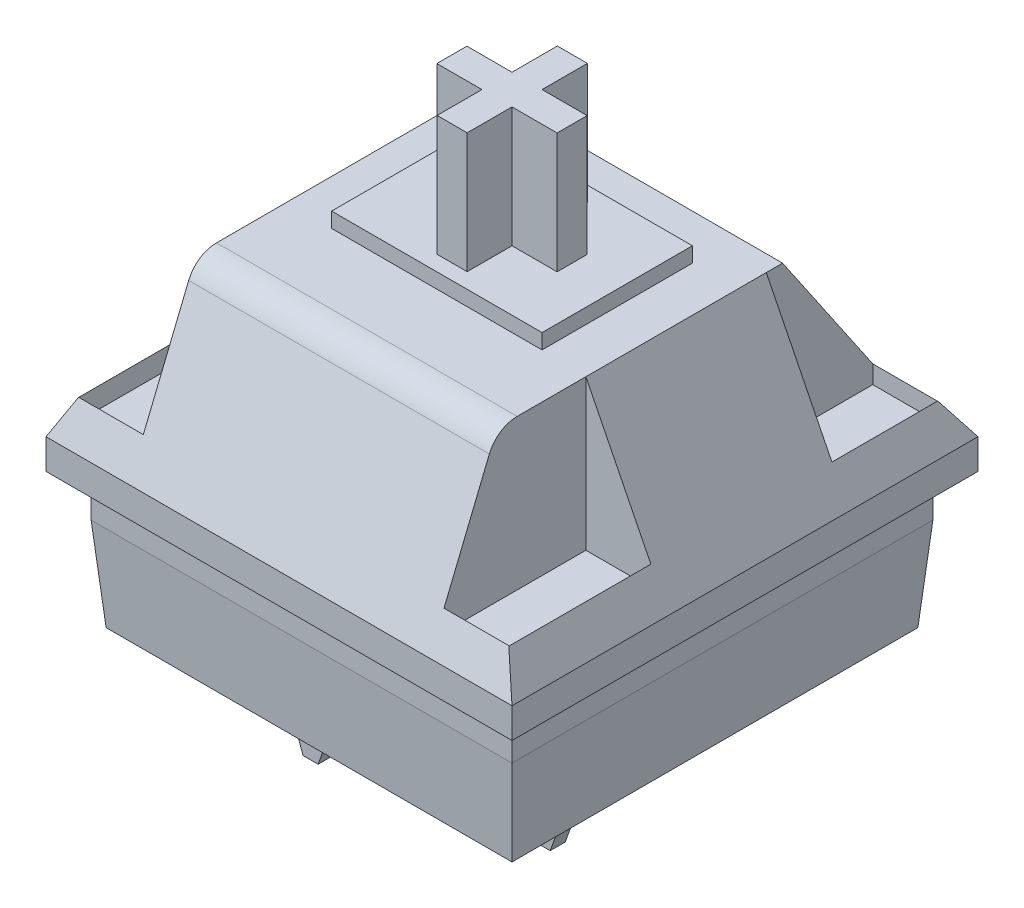
SolidWorks part; units mm, degrees
ref_plane "前视基准面" through (0, 0, 0) normal (0, 0, 1) x (1, 0, 0)
ref_plane "上视基准面" through (0, 0, 0) normal (0, 1, 0) x (1, 0, 0)
ref_plane "右视基准面" through (0, 0, 0) normal (1, 0, 0) x (0, 0, -1)
sketch "草图1" plane through (0, 0, 0) normal (0, 1, 0) x (1, 0, 0)
  line L1 (-6.75, 6.75) -> (6.75, 6.75)
  line L2 (-6.75, 6.75) -> (-6.75, -6.75)
  line L3 (-6.75, -6.75) -> (6.75, -6.75)
  line L4 (6.75, 6.75) -> (6.75, -6.75)
  line L5 (-6.75, 6.75) -> (6.75, -6.75) construction
  line L6 (-6.75, -6.75) -> (6.75, 6.75) construction
  point P0 (0, 0)
  dimension "D1" = 13.5
  dimension "D2" = 13.5
ref_plane "基准面1" through (0, 4.5, 0) normal (0, 1, 0) x (1, 0, 0)
sketch "草图2" plane through (0, 4.5, 0) normal (0, 1, 0) x (1, 0, 0)
  line L1 (-7, 7) -> (7, 7)
  line L2 (-7, 7) -> (-7, -7)
  line L3 (-7, -7) -> (7, -7)
  line L4 (7, 7) -> (7, -7)
  line L5 (-7, 7) -> (7, -7) construction
  line L6 (-7, -7) -> (7, 7) construction
  point P0 (0, 0)
  dimension "D1" = 14
  dimension "D2" = 14
ref_plane "基准面2" through (0, -0.3738, -6.7292) normal (0, -0.0555, -0.9985) x (-1, 0, 0)
extrude "凸台-拉伸1" add sketch "草图2" against normal blind 1.4
loft "放样2" add profiles "草图1" section face at (0, 3.1, 0) section "草图1"
sketch "草图8" plane through (0, 4.5, 0) normal (0, 1, 0) x (1, 0, 0)
  line L1 (7.75, -7.75) -> (-7.75, -7.75)
  line L2 (7.75, -7.75) -> (7.75, 7.75)
  line L3 (7.75, 7.75) -> (-7.75, 7.75)
  line L4 (-7.75, -7.75) -> (-7.75, 7.75)
  line L5 (7.75, -7.75) -> (-7.75, 7.75) construction
  line L6 (7.75, 7.75) -> (-7.75, -7.75) construction
  point P0 (0, 0)
  dimension "D1" = 15.5
  dimension "D2" = 15.5
extrude "凸台-拉伸2" add sketch "草图8" along normal blind 1
ref_plane "基准面8" through (0, 11, 0) normal (0, 1, 0) x (1, 0, 0)
sketch "草图10" plane through (0, 11, 0) normal (0, 1, 0) x (1, 0, 0)
  line L0 (-5, 0) -> (5, 0) construction
  line L1 (-5, 4) -> (5, 4)
  line L2 (-5, 4) -> (-5, -5.5)
  line L3 (-5, -5.5) -> (5, -5.5)
  line L4 (5, 4) -> (5, -5.5)
  point P4 (0, 0)
  point P5 (0, 0)
  dimension "D1" = 10
  dimension "D2" = 5.5
  dimension "D3" = 4
loft "放样6" add profiles "草图10" section face at (0, 5.5, 0) section "草图10"
ref_plane "基准面9" through (0, 11, 0) normal (0, 1, 0) x (1, 0, 0)
sketch "草图12" plane through (0, 11, 0) normal (0, 1, 0) x (1, 0, 0)
  line L1 (-3.5, -2.5) -> (3.5, -2.5)
  line L2 (-3.5, -2.5) -> (-3.5, 2.5)
  line L3 (-3.5, 2.5) -> (3.5, 2.5)
  line L4 (3.5, -2.5) -> (3.5, 2.5)
  line L5 (-3.5, -2.5) -> (3.5, 2.5) construction
  line L6 (-3.5, 2.5) -> (3.5, -2.5) construction
  point P0 (0, 0)
  dimension "D1" = 5
  dimension "D2" = 7
extrude "凸台-拉伸3" add sketch "草图12" along normal blind 0.5
ref_plane "基准面10" through (0, 11.5, 0) normal (0, 1, 0) x (1, 0, 0)
sketch "草图14" plane through (0, 11.5, 0) normal (0, 1, 0) x (1, 0, 0)
  line L0 (0, 2.7022) -> (0, 2.0086) construction
  line L1 (-3.5, 0) -> (-2, 0) construction
  line L2 (-3.5, 2.5) -> (-3.5, -2.5) construction
  line L3 (3.5, -2.5) -> (3.5, 2.5) construction
  line L4 (0.5, -0.5) -> (2, -0.5)
  line L5 (-0.5, 2.0086) -> (0.5, 2.0086)
  line L6 (-0.5, -0.5) -> (-0.5, -1.9914)
  line L7 (-0.5, -1.9914) -> (0.5, -1.9914)
  line L8 (0.5, -0.5) -> (0.5, -1.9914)
  line L9 (0, 0.0086) -> (0.0023, -0.0006) construction
  line L10 (-0.0023, -0.0006) -> (0, 0.0086) construction
  line L11 (-2, 0.5) -> (-0.5, 0.5)
  line L12 (-2, 0.5) -> (-2, -0.5)
  line L13 (-2, -0.5) -> (-0.5, -0.5)
  line L14 (2, 0.5) -> (2, -0.5)
  line L15 (-0.002, 0.0005) -> (0.0023, -0.0006) construction
  line L16 (-0.0023, -0.0006) -> (0.002, 0.0005) construction
  line L17 (-0.5, 2.0086) -> (-0.5, 0.5)
  line L18 (0.5, 2.0086) -> (0.5, 0.5)
  line L21 (0, 0.0086) -> (0, 0) construction
  line L22 (2, 0) -> (3.5, 0) construction
  line L23 (0, -1.9914) -> (0, -2.685) construction
  line L24 (-0.0022, 0) -> (0.0022, 0) construction
  line L25 (0.5, 0.5) -> (2, 0.5)
  point P9 (0, 0.0086)
  point P14 (0, 0)
  dimension "D1" = 1
  dimension "D2" = 4
  dimension "D3" = 1
  dimension "D4" = 4
extrude "凸台-拉伸5" add sketch "草图14" along normal blind 4
ref_plane "基准面11" through (0, 0, 0) normal (0, -1, 0) x (-1, 0, 0)
sketch "草图16" plane through (0, 0, 0) normal (0, -1, 0) x (-1, 0, 0)
  circle A0 centre (0, 0) radius 2
  dimension "D1" = 4
extrude "凸台-拉伸6" add sketch "草图16" along normal blind 3
chamfer "倒角1" distance 0.25 angle 70 1 edges at (0, -3, -2)
sketch "草图18" plane through (0, 11, 0) normal (0, 1, 0) x (1, 0, 0)
  line L0 (0, 0) -> (0, 12.7967) construction
  line L1 (5, 4) -> (-5, 4) construction
  line L2 (-4, 7) -> (4, 7)
  line L3 (-4, 7) -> (-4, 4)
  line L4 (-4, 4) -> (4, 4)
  line L5 (4, 7) -> (4, 4)
  line L6 (-4, 7) -> (4, 4) construction
  line L7 (-4, 4) -> (4, 7) construction
  point P3 (0, 5.5)
  dimension "D1" = 8
  dimension "D2" = 3
extrude "切除-拉伸1" cut sketch "草图18" against normal blind 4.5
sketch "草图20" plane through (0, 11, 0) normal (0, 1, 0) x (1, 0, 0)
  line L1 (5, 3.4576) -> (7.1838, 3.4576)
  line L2 (5, 3.4576) -> (5, 7)
  line L3 (5, 7) -> (7.1838, 7)
  line L4 (7.1838, 3.4576) -> (7.1838, 7)
  line L5 (0, -8.525) -> (0, 8.525) construction
  line L6 (-5, 7) -> (-7.1838, 7)
  line L7 (-7.1838, 3.4576) -> (-7.1838, 7)
  line L8 (-5, 3.4576) -> (-7.1838, 3.4576)
  line L9 (-5, 3.4576) -> (-5, 7)
  dimension "D1" = 2.1838
sketch "草图23" plane through (0, 11, 0) normal (0, 1, 0) x (1, 0, 0)
  line L0 (5, -5.5) -> (5, 4) construction
  line L1 (5, -2.5424) -> (7.16, -2.5424)
  line L2 (5, -2.5424) -> (5, -7.2625)
  line L3 (5, -7.2625) -> (7.16, -7.2625)
  line L4 (7.16, -2.5424) -> (7.16, -7.2625)
  line L5 (0, -8.525) -> (0, 8.525) construction
  line L6 (-5, -7.2625) -> (-7.16, -7.2625)
  line L7 (-7.16, -2.5424) -> (-7.16, -7.2625)
  line L8 (-5, -2.5424) -> (-7.16, -2.5424)
  line L9 (-5, -2.5424) -> (-5, -7.2625)
  dimension "D2" = 2.16
extrude "切除-拉伸9" cut sketch "草图20" against normal blind 5
extrude "切除-拉伸10" cut sketch "草图23" against normal blind 5
sketch "草图26" plane through (0, 11, 0) normal (0, 1, 0) x (1, 0, 0)
  line L0 (-4, 4) -> (4, 4) construction
  line L1 (0, 4) -> (0, 8.3854) construction
  circle A0 centre (0, 5.526) radius 1.5
  dimension "D1" = 3
extrude "切除-拉伸12" cut sketch "草图26" against normal blind 5.5
sketch "草图27" plane through (0, 0, 0) normal (0, 1, 0) x (1, 0, 0)
  line L0 (0, 0) -> (0, -2.54) construction
  line L1 (0, -2.54) -> (3.81, -2.54) construction
  line L2 (0, 0) -> (0, -3.91) construction
  line L3 (0, -3.91) -> (-2.54, -3.91) construction
  line L5 (-3.04, -4.16) -> (-2.04, -4.16)
  line L6 (-3.04, -4.16) -> (-3.04, -3.66)
  line L7 (-3.04, -3.66) -> (-2.04, -3.66)
  line L8 (-2.04, -4.16) -> (-2.04, -3.66)
  line L9 (-3.04, -4.16) -> (-2.04, -3.66) construction
  line L10 (-3.04, -3.66) -> (-2.04, -4.16) construction
  line L11 (3.31, -2.79) -> (4.31, -2.79)
  line L12 (3.31, -2.79) -> (3.31, -2.29)
  line L13 (3.31, -2.29) -> (4.31, -2.29)
  line L14 (4.31, -2.79) -> (4.31, -2.29)
  line L15 (3.31, -2.79) -> (4.31, -2.29) construction
  line L16 (3.31, -2.29) -> (4.31, -2.79) construction
  dimension "D1" = 2.54
  dimension "D2" = 3.81
  dimension "D3" = 3.91
  dimension "D4" = 2.54
  dimension "D5" = 0.5
  dimension "D6" = 1
  dimension "D7" = 0.5
  dimension "D8" = 1
extrude "凸台-拉伸7" add sketch "草图27" against normal blind 3
chamfer "倒角2" distance 0.25 angle 70 2 edges at (3.31, -3, 2.54) (4.31, -3, 2.54)
chamfer "倒角3" distance 0.25 angle 70 2 edges at (-2.04, -3, 3.91) (-3.04, -3, 3.91)
fillet "圆角1" radius 1 1 edges
sketch "草图25" plane through (0, 11, 0) normal (0, 1, 0) x (1, 0, 0)
  line L0 (0, 0) -> (0, 10.3553) construction
  line L2 (-5, 4) -> (5, 4) construction
  circle A0 centre (0, 5.5) radius 1.5
  dimension "D1" = 3
